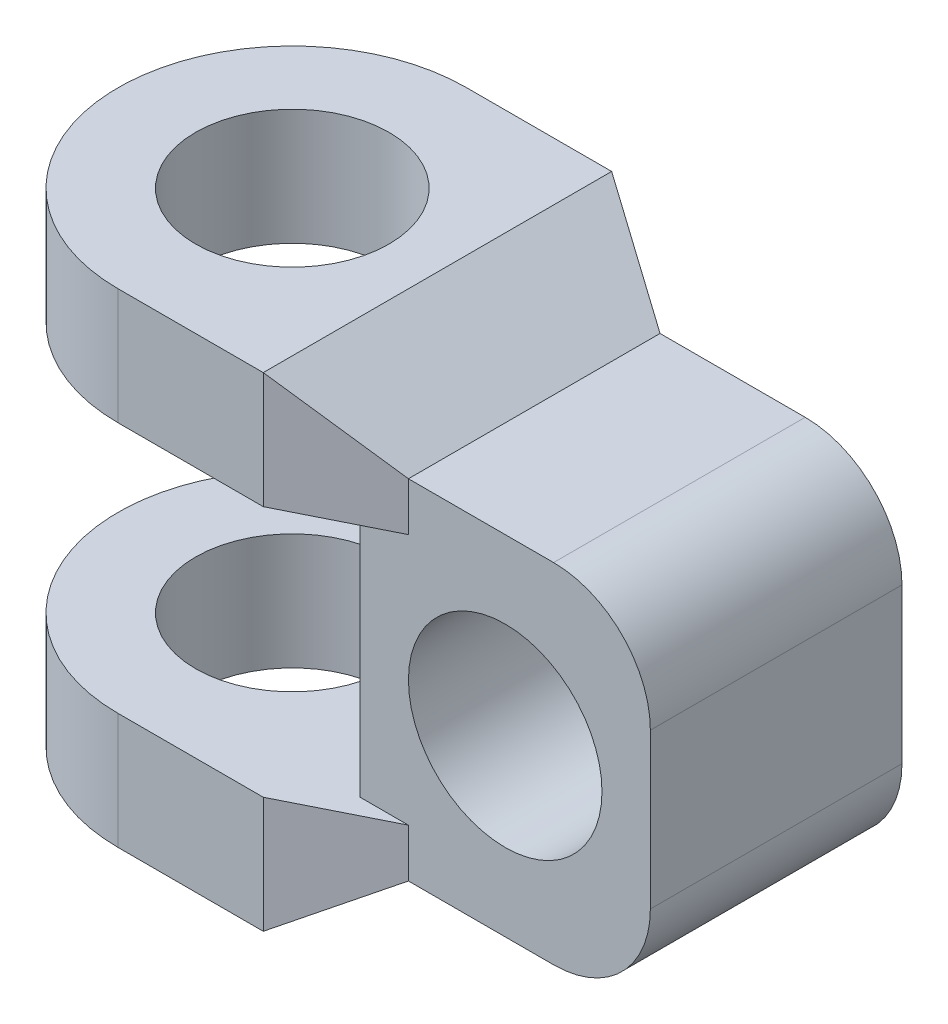
SolidWorks part; units mm, degrees
ref_plane "Front Plane" through (0, 0, 0) normal (0, 0, 1) x (1, 0, 0)
ref_plane "Top Plane" through (0, 0, 0) normal (0, 1, 0) x (1, 0, 0)
ref_plane "Right Plane" through (0, 0, 0) normal (1, 0, 0) x (0, 0, -1)
sketch "Sketch1" plane through (0, 0, 0) normal (0, 1, 0) x (1, 0, 0)
  line L0 (0, 18) -> (50, 18)
  line L1 (50, 18) -> (50, -18)
  line L2 (50, -18) -> (0, -18)
  circle A0 centre (0, 0) radius 10
  arc A2 (0, 18) -> (0, -18) centre (0, 0) ccw
  dimension "D1" = 50
  dimension "D2" = 18
  dimension "D3" = 20
extrude "Boss-Extrude1" add sketch "Sketch1" along normal blind 50
sketch "Sketch2" plane through (0, 0, -18) normal (0, 0, -1) x (-1, 0, 0)
  line L1 (-20, 12) -> (24.1167, 12)
  line L2 (-20, 12) -> (-20, 38)
  line L3 (-20, 38) -> (24.1167, 38)
  line L4 (24.1167, 12) -> (24.1167, 38)
  line L6 (0, 0) -> (18, 0) construction
  line L7 (18, 50) -> (0, 50) construction
  line L8 (-50, 50) -> (-50, 0) construction
  dimension "D1" = 12
  dimension "D2" = 12
  dimension "D3" = 30
extrude "Cut-Extrude1" cut sketch "Sketch2" against normal blind 50
sketch "Sketch3" plane through (0, 0, -18) normal (0, 0, -1) x (-1, 0, 0)
  line L0 (-50, 50) -> (0, 50) construction
  line L1 (-50, 50) -> (-50, 0) construction
  circle A0 centre (-35, 25) radius 10
  dimension "D1" = 25
  dimension "D2" = 15
extrude "Cut-Extrude2" cut sketch "Sketch3" against normal blind 50
sketch "Sketch4" plane through (0, 0, -18) normal (0, 0, -1) x (-1, 0, 0)
  line L0 (0, 12) -> (0, 0) construction
  line L1 (-50, 0) -> (0, 0) construction
  line L2 (-15, 0) -> (-25, 7)
  line L3 (-25, 7) -> (-50, 7)
  line L4 (-50, 50) -> (-50, 0) construction
  line L5 (-50, 7) -> (-50, 0)
  line L6 (-50, 0) -> (-15, 0)
  line L7 (-50, 50) -> (-50, 43)
  line L8 (-50, 43) -> (-25, 43)
  line L9 (-25, 43) -> (-15, 50)
  line L10 (-50, 50) -> (0, 50) construction
  line L11 (-15, 50) -> (-50, 50)
  dimension "D1" = 15
  dimension "D2" = 10
  dimension "D3" = 7
  dimension "D4" = 7
  dimension "D5" = 10
  dimension "D6" = 15
extrude "Cut-Extrude3" cut sketch "Sketch4" against normal blind 36
sketch "Sketch5" plane through (0, 50, 0) normal (0, 1, 0) x (1, 0, 0)
  line L0 (15, 18) -> (25, 13)
  line L1 (25, 13) -> (50, 13)
  line L2 (15, 18) -> (50, 18)
  line L3 (50, 18) -> (50, 13)
  line L4 (15, -18) -> (25, -13)
  line L5 (25, -13) -> (50, -13)
  line L6 (15, -18) -> (50, -18)
  line L7 (50, -18) -> (50, -13)
  dimension "D1" = 35
  dimension "D2" = 35
  dimension "D3" = 5
  dimension "D4" = 5
  dimension "D5" = 10
  dimension "D6" = 10
extrude "Cut-Extrude4" cut sketch "Sketch5" against normal blind 50
fillet "Fillet1" radius 10 2 edges at (50, 43, 0) (50, 7, 0)
sketch "Sketch6" plane through (20, 0, 0) normal (-1, 0, 0) x (0, 0, 1)
  line L0 (15.5, 12) -> (-15.5, 12) construction
  line L1 (-15.5, 38) -> (-13, 38)
  line L2 (-15.5, 38) -> (-15.5, 12)
  line L3 (-15.5, 12) -> (-13, 12)
  line L4 (-13, 38) -> (-13, 12)
  line L6 (15.5, 38) -> (13, 38)
  line L7 (15.5, 38) -> (15.5, 12)
  line L8 (15.5, 12) -> (13, 12)
  line L9 (13, 38) -> (13, 12)
  dimension "D1" = 2.5
  dimension "D2" = 2.5
extrude "Cut-Extrude5" cut sketch "Sketch6" against normal blind 50
